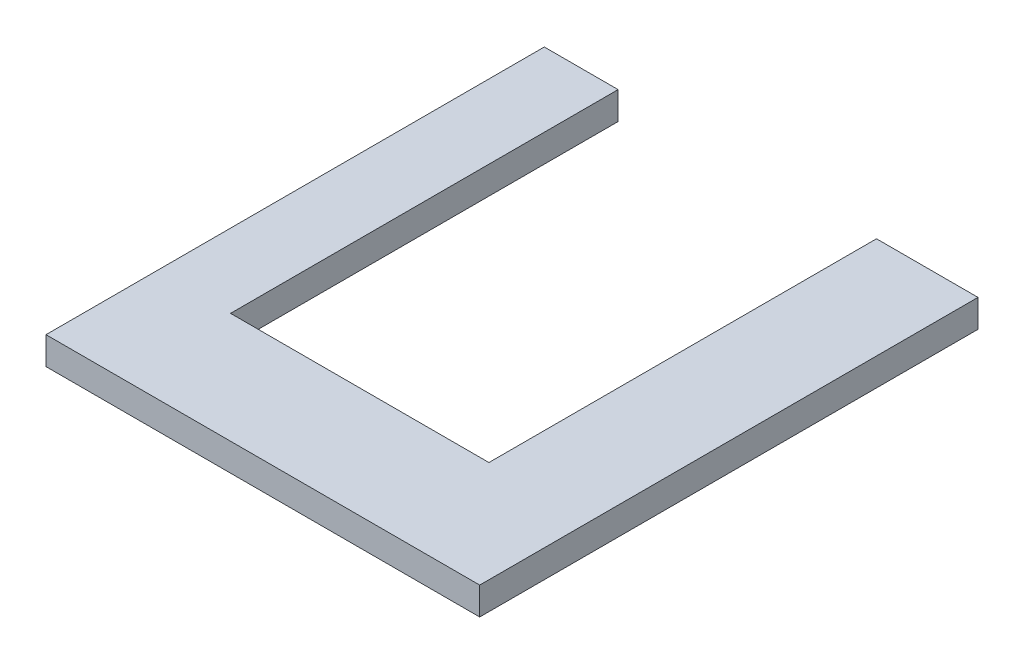
SolidWorks part; units mm, degrees
ref_plane "Plano frontal" through (0, 0, 0) normal (0, 0, 1) x (1, 0, 0)
ref_plane "Plano superior" through (0, 0, 0) normal (0, 1, 0) x (1, 0, 0)
ref_plane "Plano direito" through (0, 0, 0) normal (1, 0, 0) x (0, 0, -1)
sketch "Esboço1" plane through (0, 0, 0) normal (0, 0, 1) x (1, 0, 0)
  line L1 (0, 0) -> (2350, 0)
  line L2 (0, 0) -> (0, 150)
  line L3 (0, 150) -> (2350, 150)
  line L4 (2350, 0) -> (2350, 150)
  dimension "D1" = 150
  dimension "D2" = 2350
extrude "Ressalto-extrusão1" add sketch "Esboço1" along normal blind 2700
sketch "Esboço2" plane through (0, 150, 0) normal (0, 1, 0) x (1, 0, 0)
  line L1 (400, 0) -> (1800, 0)
  line L2 (400, 0) -> (400, -2100)
  line L3 (400, -2100) -> (1800, -2100)
  line L4 (1800, 0) -> (1800, -2100)
  line L5 (2350, -2700) -> (2350, 0) construction
  line L6 (2350, 0) -> (0, 0) construction
  dimension "D1" = 1400
  dimension "D2" = 2100
  dimension "D3" = 550
  dimension "D4" = 0
extrude "Corte-extrusão1" cut sketch "Esboço2" against normal through all
